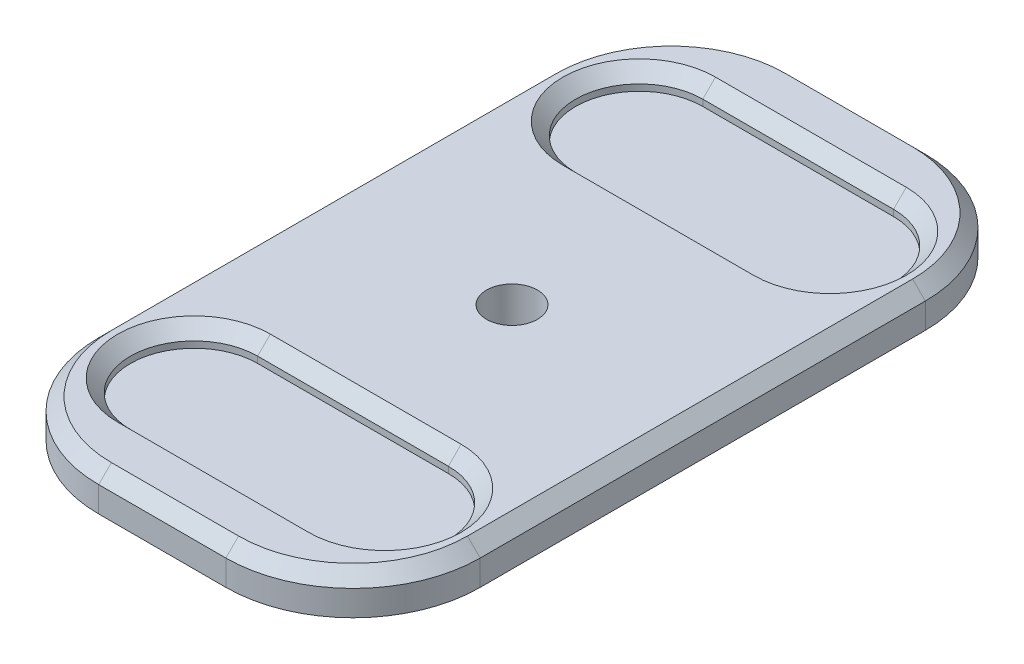
SolidWorks part; units mm, degrees
ref_plane "Front Plane" through (0, 0, 0) normal (0, 0, 1) x (1, 0, 0)
ref_plane "Top Plane" through (0, 0, 0) normal (0, 1, 0) x (1, 0, 0)
ref_plane "Right Plane" through (0, 0, 0) normal (1, 0, 0) x (0, 0, -1)
sketch "Sketch1" plane through (0, 0, 0) normal (0, 1, 0) x (1, 0, 0)
  line L0 (-30, 0) -> (30, 0)
  line L2 (-30, 0) -> (-30, -70)
  line L3 (-30, -70) -> (30, -70)
  line L4 (30, 0) -> (30, -70)
  line L5 (0, 0) -> (7.7586, -18.1034) construction
  line L6 (-30, -70) -> (-15, -35) construction
  line L7 (-15, -35) -> (15, -35)
  line L9 (-15, -15) -> (15, -15)
  line L10 (15, -35) -> (18.5107, -43.1916) construction
  line L13 (18.5107, -43.1916) -> (15, -15) construction
  line L14 (-6.4286, -15) -> (0, 0) construction
  line L15 (20.152, -47.0214) -> (30, -70) construction
  arc A0 (-15, -15) -> (-15, -35) centre (-15, -25) ccw
  arc A1 (15, -35) -> (15, -15) centre (15, -25) ccw
  point P0 (0, 0)
  point P6 (15, -20)
  point P7 (0, -25)
  dimension "D1" = 60
  dimension "D3" = 15
  dimension "D4" = 30
  dimension "D6" = 20
extrude "Boss-Extrude1" add sketch "Sketch1" along normal blind 3
mirror "Mirror1" about plane through (-30, 3, 70) normal (0, 0, -1) of "Boss-Extrude1"
sketch "Sketch2" plane through (0, 0, 0) normal (0, -1, 0) x (-1, 0, 0)
  line L1 (30, -140) -> (-30, -140)
  line L2 (30, -140) -> (30, 0)
  line L3 (30, 0) -> (-30, 0)
  line L4 (-30, -140) -> (-30, 0)
extrude "Boss-Extrude2" add sketch "Sketch2" along normal blind 3
sketch "Sketch4" plane through (0, 3, 0) normal (0, 1, 0) x (1, 0, 0)
  line L1 (-30, -5) -> (30, -5)
  line L2 (-30, -5) -> (-30, 0)
  line L3 (-30, 0) -> (30, 0)
  line L4 (30, -5) -> (30, 0)
  line L5 (-30, -5) -> (30, 0) construction
  line L6 (-30, 0) -> (30, -5) construction
  line L7 (-30, -135) -> (30, -135)
  line L8 (-30, -135) -> (-30, -140)
  line L9 (-30, -140) -> (30, -140)
  line L10 (30, -135) -> (30, -140)
  line L11 (-30, -135) -> (30, -140) construction
  line L12 (-30, -140) -> (30, -135) construction
  point P0 (0, -2.5)
  point P6 (0, -137.5)
  dimension "D1" = 5
  dimension "D2" = 5
extrude "Cut-Extrude1" cut sketch "Sketch4" against normal blind 10
chamfer "Chamfer2" distance 15 angle 45 4 edges at (-30, 0, 135) (30, 0, 135) (30, 0, 5) (-30, 0, 5)
sketch "Sketch5" plane through (0, -3, 0) normal (0, -1, 0) x (1, 0, 0)
  line L0 (15, 5) -> (-15, 5) construction
  circle A0 centre (0, 70) radius 4
  dimension "D1" = 65
extrude "Cut-Extrude2" cut sketch "Sketch5" against normal blind 3
fillet "Fillet3" radius 20 8 edges at (30, 0, 20) (15, 0, 5) (-15, 0, 5) (-30, 0, 20) (30, 0, 120) (15, 0, 135) (-30, 0, 120) (-15, 0, 135)
chamfer "Chamfer3" distance 1 angle 45 24 edges at (0, 3, 105) (-25, 3, 115) (0, 3, 125) (25, 3, 115) (-25, 3, 25) (0, 3, 35) (25, 3, 25) (0, 3, 15) (28.4776, 3, 119.3694) (22.5, 3, 127.5) (14.3694, 3, 133.4776) (0, 3, 135) (-14.3694, 3, 133.4776) (-22.5, 3, 127.5) (-28.4776, 3, 119.3694) (-30, 3, 70) (-28.4776, 3, 20.6306) (-22.5, 3, 12.5) (-14.3694, 3, 6.5224) (0, 3, 5) (14.3694, 3, 6.5224) (22.5, 3, 12.5) (28.4776, 3, 20.6306) (30, 3, 70)
sketch "Sketch6" plane through (0, 3, 0) normal (0, 1, 0) x (1, 0, 0)
  line L0 (-6.7157, -5) -> (6.7157, -5) construction
  line L1 (-51.5342, -60) -> (51.6632, -60)
  line L2 (-51.5342, -60) -> (-51.5342, -147.2018)
  line L3 (-51.5342, -147.2018) -> (51.6632, -147.2018)
  line L4 (51.6632, -60) -> (51.6632, -147.2018)
  dimension "D1" = 55
extrude "Cut-Extrude3" cut sketch "Sketch6" against normal blind 100
mirror "Mirror4" about plane through (-51.5342, -97, 60) normal (0, 0, -1) of "Boss-Extrude1", "Boss-Extrude2", "Cut-Extrude1", "Cut-Extrude3"
sketch "Sketch7" plane through (0, 3, 0) normal (0, 1, 0) x (1, 0, 0)
  line L0 (30, -60) -> (30, -115) construction
  line L1 (-30, -60) -> (30, -60)
  line L2 (-30, -60) -> (-30, -5)
  line L3 (-30, -5) -> (30, -5)
  line L4 (30, -60) -> (30, -5)
  line L6 (-15, -35) -> (15, -35)
  line L8 (-15, -15) -> (15, -15)
  arc A0 (15, -35) -> (15, -15) centre (15, -25) ccw
  arc A1 (-15, -15) -> (-15, -35) centre (-15, -25) ccw
  dimension "D1" = 55
  dimension "D2" = 0
  dimension "D3" = 20
  dimension "D4" = 30
  dimension "D5" = 25
extrude "Boss-Extrude3" add sketch "Sketch7" against normal up to surface (3 mm away) up to face at (0, 0, 95)
sketch "Sketch8" plane through (0, 0, 0) normal (0, -1, 0) x (-1, 0, 0)
  line L1 (-30, -5) -> (30, -5)
  line L2 (-30, -5) -> (-30, -60)
  line L3 (-30, -60) -> (30, -60)
  line L4 (30, -5) -> (30, -60)
extrude "Boss-Extrude4" add sketch "Sketch8" along normal up to surface (3 mm away) up to face at (0, -3, 87.5)
fillet "Fillet4" radius 20 4 edges at (30, 0, 115) (-30, 0, 115) (30, 0, 5) (-30, 0, 5)
chamfer "Chamfer4" distance 2 angle 45 16 edges at (25, 3, 25) (0, 3, 15) (-25, 3, 25) (0, 3, 35) (-24.1421, 3, 109.1421) (-30, 3, 60) (-24.1421, 3, 10.8579) (0, 3, 5) (24.1421, 3, 10.8579) (30, 3, 60) (24.1421, 3, 109.1421) (0, 3, 115) (0, 3, 85) (-25, 3, 95) (0, 3, 105) (25, 3, 95)
sketch "Sketch9" plane through (0, -3, 0) normal (0, -1, 0) x (-1, 0, 0)
  circle A0 centre (0, -60) radius 4
extrude "Cut-Extrude4" cut sketch "Sketch9" against normal blind 10
equation "\"D5@Sketch1\"=(60-30)/2"
